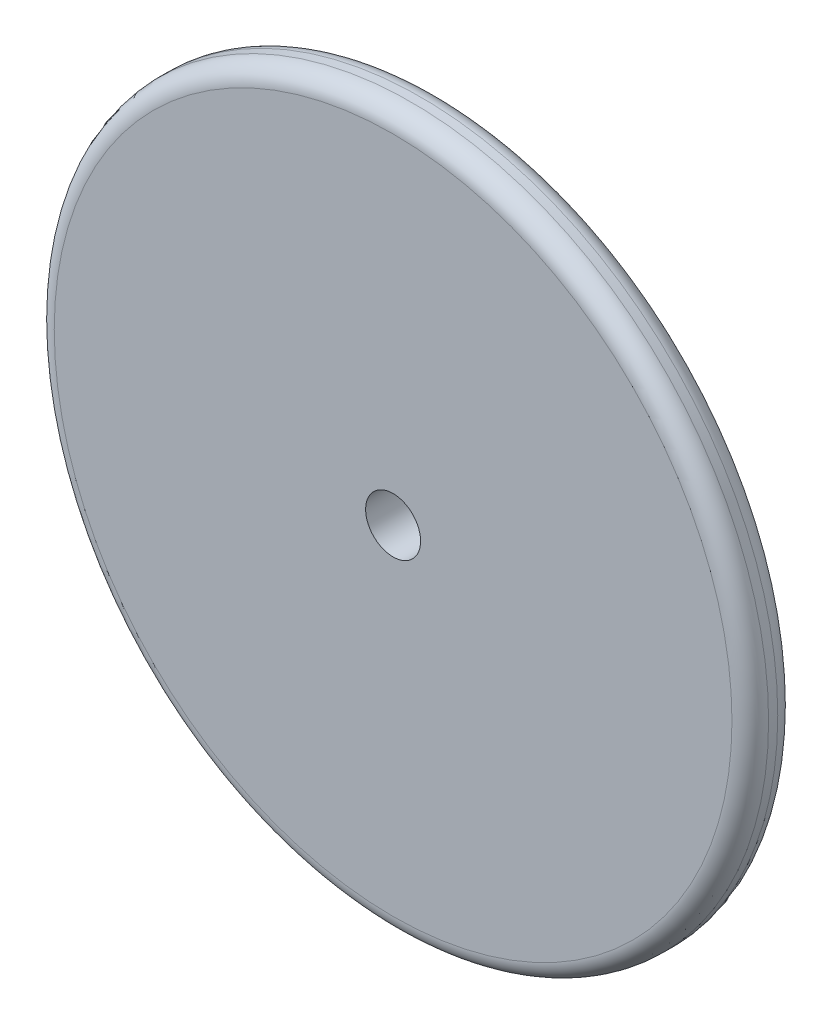
SolidWorks part; units mm, degrees
material "尼龙 101"
ref_plane "前视基准面" through (0, 0, 0) normal (0, 0, 1) x (1, 0, 0)
ref_plane "上视基准面" through (0, 0, 0) normal (0, 1, 0) x (1, 0, 0)
ref_plane "右视基准面" through (0, 0, 0) normal (1, 0, 0) x (0, 0, -1)
sketch "草图1" plane through (0, 0, 0) normal (0, 0, 1) x (1, 0, 0)
  circle A0 centre (0, 0) radius 39
  circle A1 centre (0, 0) radius 3
  dimension "D1" = 78
  dimension "D2" = 6
extrude "凸台-拉伸1" add sketch "草图1" along normal blind 5
fillet "圆角1" radius 2 2 edges at (39, 0, 0) (39, 0, 5)
